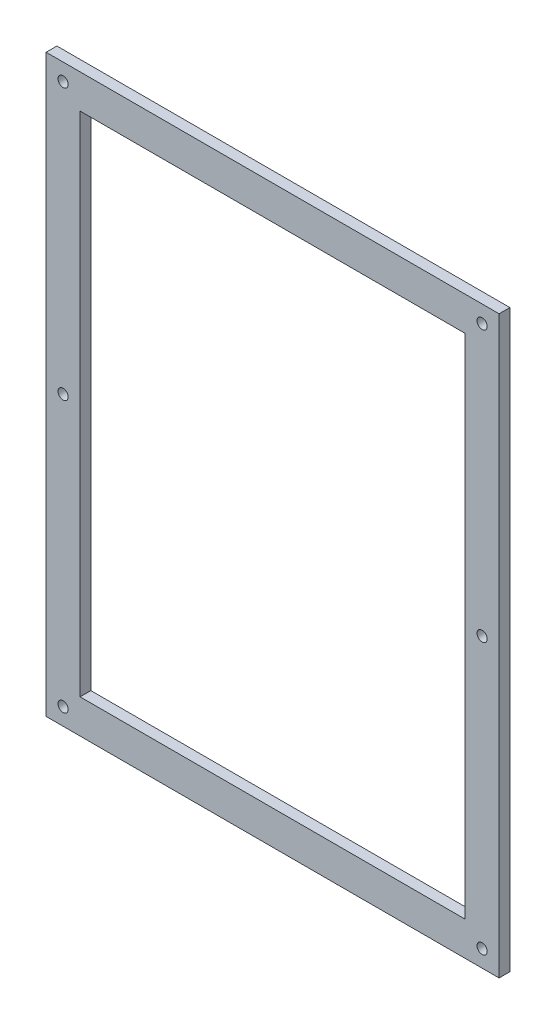
SolidWorks part; units mm, degrees
material "Acrylic (Medium-high impact)"
ref_plane "Front Plane" through (0, 0, 0) normal (0, 0, 1) x (1, 0, 0)
ref_plane "Top Plane" through (0, 0, 0) normal (0, 1, 0) x (1, 0, 0)
ref_plane "Right Plane" through (0, 0, 0) normal (1, 0, 0) x (0, 0, -1)
sketch "Sketch1" plane through (0, 0, 0) normal (0, 0, 1) x (1, 0, 0)
  line L0 (0, 0) -> (0, 169.3333)
  line L1 (0, 169.3333) -> (133.35, 169.3333)
  line L2 (133.35, 169.3333) -> (133.35, 0)
  line L3 (133.35, 0) -> (0, 0)
  line L8 (66.675, 169.3333) -> (66.675, 0) construction
  line L9 (0, 84.6667) -> (133.35, 84.6667) construction
  circle A0 centre (5, 5) radius 1.5
  circle A1 centre (5, 164.3333) radius 1.5
  circle A4 centre (5, 84.6667) radius 1.5
  circle A5 centre (128.35, 164.3333) radius 1.5
  circle A6 centre (128.35, 84.6667) radius 1.5
  circle A7 centre (128.35, 5) radius 1.5
  dimension "D7" = 3
  dimension "D10" = 3
  dimension "D1" = 169.3333
  dimension "D2" = 133.35
  dimension "D8" = 5
  dimension "D9" = 5
extrude "Boss-Extrude1" add sketch "Sketch1" along normal blind 3.175
sketch "Sketch2" plane through (0, 0, 3.175) normal (0, 0, 1) x (1, 0, 0)
  line L0 (10, 10) -> (10, 159.3333)
  line L1 (10, 159.3333) -> (123.35, 159.3333)
  line L2 (123.35, 159.3333) -> (123.35, 10)
  line L3 (123.35, 10) -> (10, 10)
  line L4 (0, 0) -> (133.35, 0) construction
  line L5 (0, 169.3333) -> (0, 0) construction
  line L6 (133.35, 0) -> (133.35, 169.3333) construction
  line L7 (133.35, 169.3333) -> (0, 169.3333) construction
  dimension "D1" = 10
  dimension "D2" = 10
  dimension "D3" = 10
  dimension "D4" = 10
extrude "Cut-Extrude1" cut sketch "Sketch2" against normal up to surface (3.175 mm away) up to face at (126.85, 84.6667, 0)
equation "\"D1@Sketch1\" = 254.00 * (1/3)"
